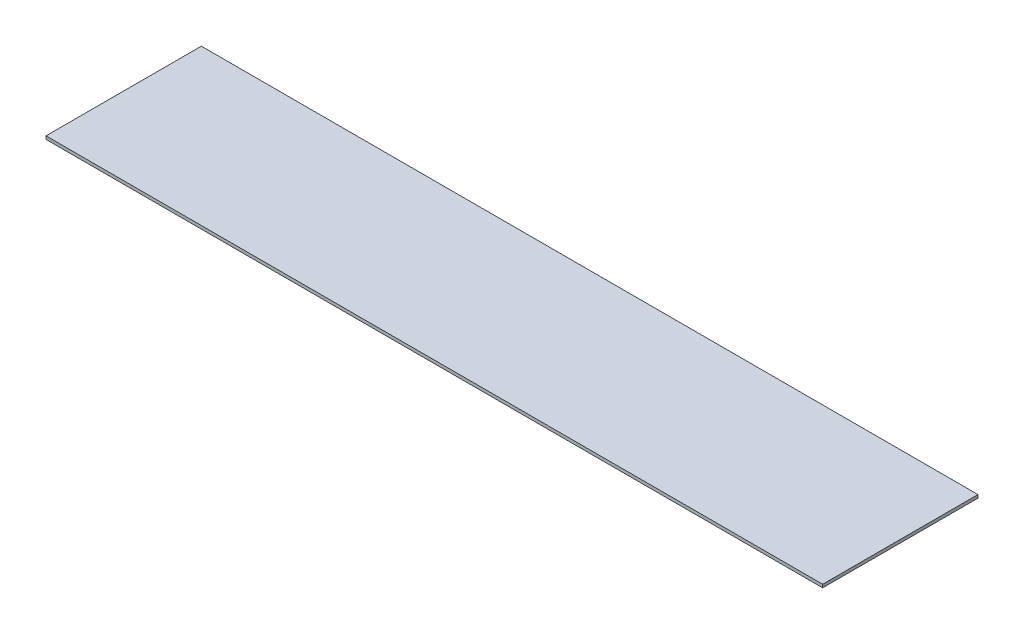
SolidWorks part; units mm, degrees
ref_plane "Alzado" through (0, 0, 0) normal (0, 0, 1) x (1, 0, 0)
ref_plane "Planta" through (0, 0, 0) normal (0, 1, 0) x (1, 0, 0)
ref_plane "Vista lateral" through (0, 0, 0) normal (1, 0, 0) x (0, 0, -1)
sketch "Croquis1" plane through (0, 0, 0) normal (0, 1, 0) x (1, 0, 0)
  line L1 (-25, -5) -> (25, -5)
  line L2 (-25, -5) -> (-25, 5)
  line L3 (-25, 5) -> (25, 5)
  line L4 (25, -5) -> (25, 5)
  line L5 (-25, -5) -> (25, 5) construction
  line L6 (-25, 5) -> (25, -5) construction
  point P0 (0, 0)
  dimension "D1" = 50
  dimension "D2" = 10
extrude "Saliente-Extruir1" add sketch "Croquis1" along normal blind 0.2
